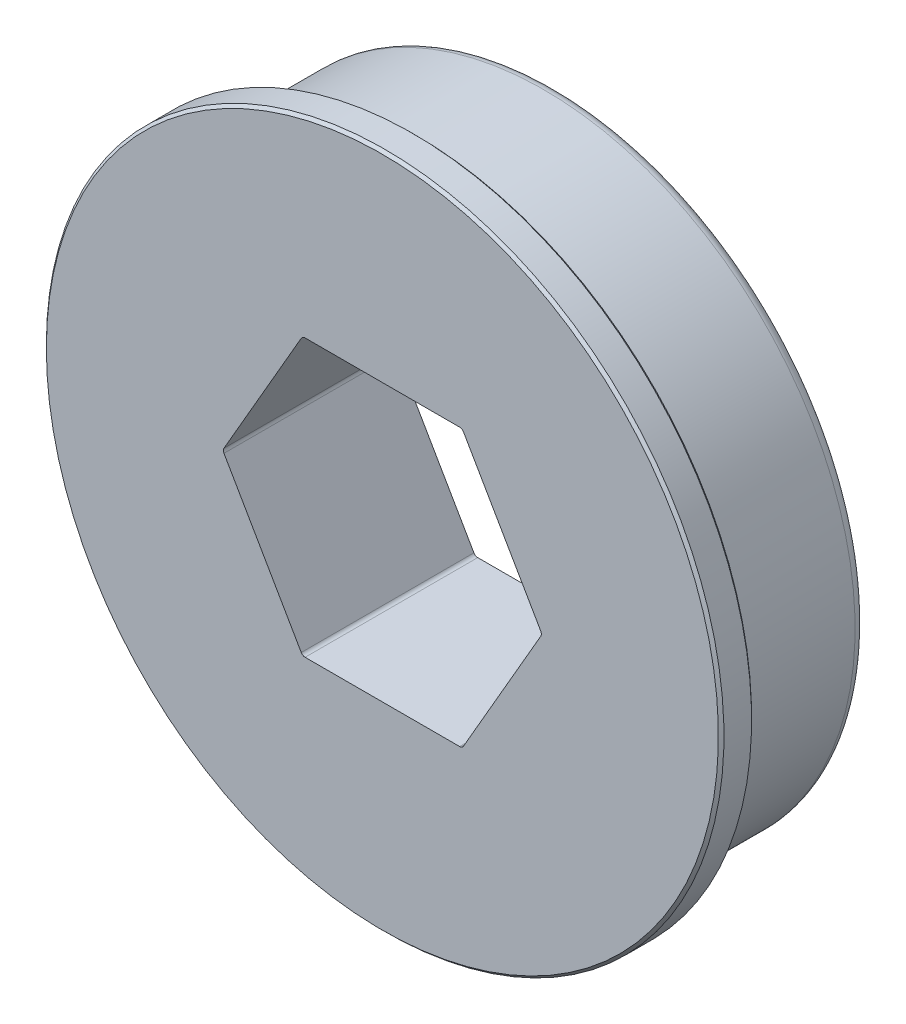
SolidWorks part; units mm, degrees
ref_plane "Front Plane" through (0, 0, 0) normal (0, 0, 1) x (1, 0, 0)
ref_plane "Top Plane" through (0, 0, 0) normal (0, 1, 0) x (1, 0, 0)
ref_plane "Right Plane" through (0, 0, 0) normal (1, 0, 0) x (0, 0, -1)
ref_plane "Plane1" through (0, 0, 0) normal (0, -1, 0) x (1, 0, 0)
sketch "Sketch1" plane through (0, 0, 0) normal (0, -1, 0) x (1, 0, 0)
  line L0 (15.4305, 7.9273) -> (0, 7.9273)
  line L1 (0, 7.9273) -> (0, 0)
  line L2 (0, 0) -> (14.2875, 0)
  line L3 (14.2875, 0) -> (14.2875, 5.8953)
  line L4 (14.2875, 5.8953) -> (13.97, 5.8953)
  line L5 (13.97, 5.8953) -> (13.97, 6.4033)
  line L6 (13.97, 6.4033) -> (15.5575, 6.4033)
  line L7 (15.5575, 6.4033) -> (15.5575, 7.8003)
  line L8 (15.5575, 7.8003) -> (15.4305, 7.9273)
  line L9 (0, 7.9273) -> (0, 0) construction
revolve "Revolve1" add sketch "Sketch1" angle 360 about L9
sketch "Sketch2" plane through (0, 0, 7.9273) normal (0, 0, 1) x (1, 0, 0)
  line L0 (3.6662, -6.35) -> (7.3323, 0)
  line L1 (7.3323, 0) -> (3.6662, 6.35)
  line L2 (3.6662, 6.35) -> (-3.6662, 6.35)
  line L3 (-3.6662, 6.35) -> (-7.3323, 0)
  line L4 (-7.3323, 0) -> (-3.6662, -6.35)
  line L5 (-3.6662, -6.35) -> (3.6662, -6.35)
extrude "Cut-Extrude1" cut sketch "Sketch2" against normal through all
chamfer "Chamfer1" distance 0.127 angle 45 1 edges at (-15.5575, 0, 6.4033)
fillet "Fillet1" radius 0.2032 6 edges at (7.3323, 0, 3.9637) (3.6662, 6.35, 3.9637) (-3.6662, -6.35, 3.9637) (3.6662, -6.35, 3.9637) (-7.3323, 0, 3.9637) (-3.6662, 6.35, 3.9637)
fillet "Fillet2" radius 0.508 1 edges at (-14.2875, 0, 0)
